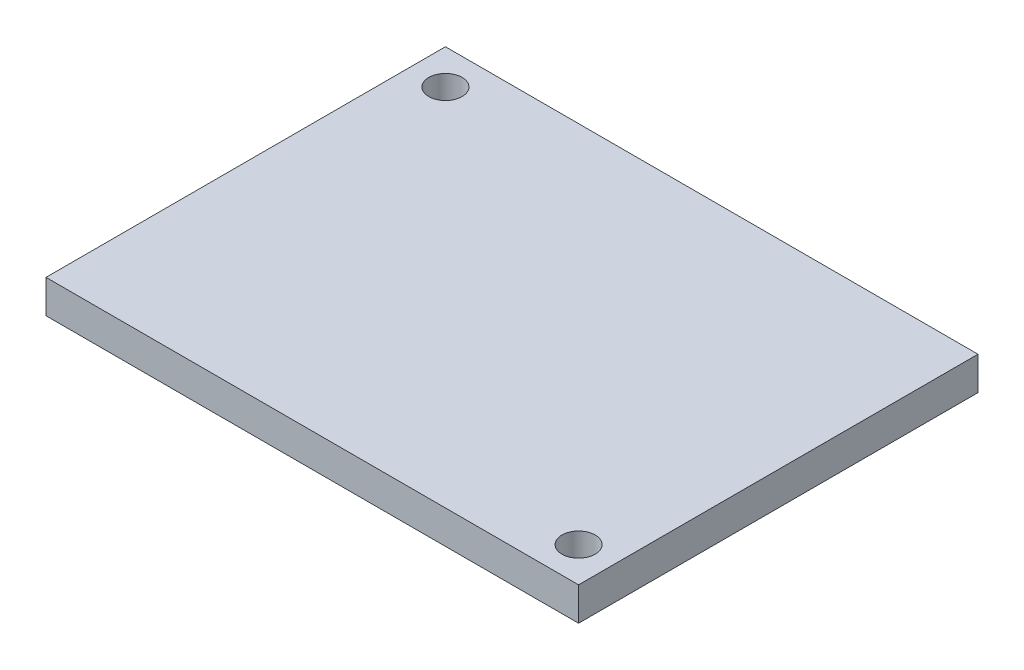
SolidWorks part; units mm, degrees
ref_plane "Front Plane" through (0, 0, 0) normal (0, 0, 1) x (1, 0, 0)
ref_plane "Top Plane" through (0, 0, 0) normal (0, 1, 0) x (1, 0, 0)
ref_plane "Right Plane" through (0, 0, 0) normal (1, 0, 0) x (0, 0, -1)
sketch "Sketch1" plane through (0, 0, 0) normal (0, 1, 0) x (1, 0, 0)
  line L0 (-22.0751, 15.7251) -> (-22.0751, 19.05) construction
  line L1 (-25.4, -19.05) -> (25.4, -19.05)
  line L2 (-25.4, -19.05) -> (-25.4, 19.05)
  line L3 (-25.4, 19.05) -> (25.4, 19.05)
  line L4 (25.4, -19.05) -> (25.4, 19.05)
  line L5 (-25.4, -19.05) -> (25.4, 19.05) construction
  line L6 (-25.4, 19.05) -> (25.4, -19.05) construction
  line L7 (-22.0751, 15.7251) -> (-25.4, 15.7251) construction
  line L8 (22.0751, -15.7251) -> (25.4, -15.7251) construction
  line L9 (22.0751, -15.7251) -> (22.0751, -19.05) construction
  circle A0 centre (-22.0751, 15.7251) radius 1.5875
  circle A1 centre (22.0751, -15.7251) radius 1.5875
  point P0 (0, 0)
  dimension "D3" = 3.175
  dimension "D4" = 3.175
  dimension "D1" = 38.1
  dimension "D2" = 50.8
  dimension "D5" = 3.3249
extrude "Boss-Extrude1" add sketch "Sketch1" along normal blind 3.175
